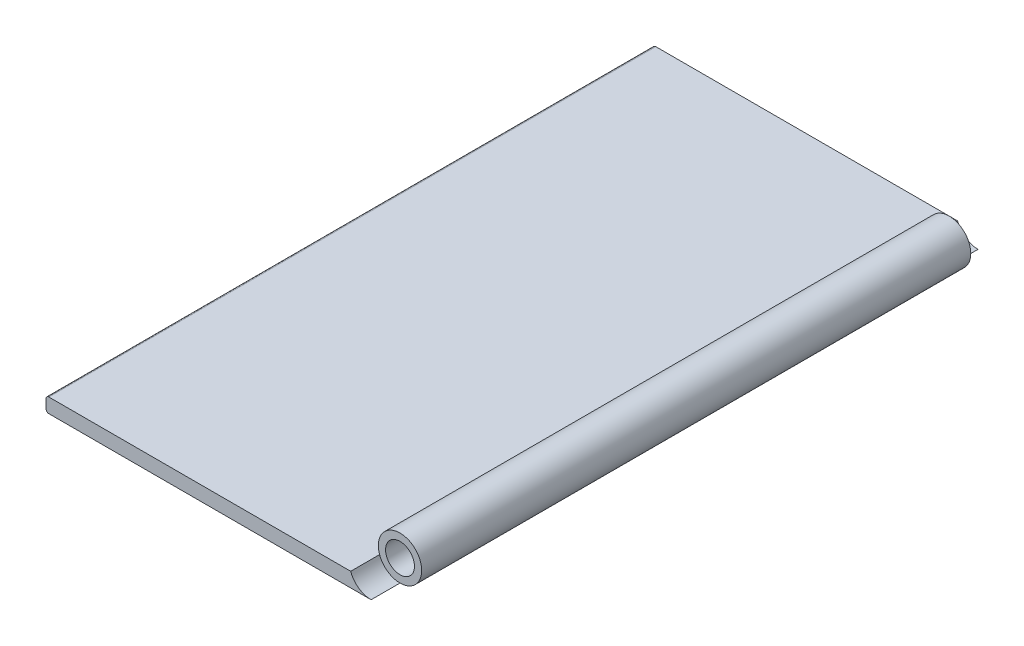
SolidWorks part; units mm, degrees
ref_plane "Front" through (0, 0, 0) normal (0, 0, 1) x (1, 0, 0)
ref_plane "Top" through (0, 0, 0) normal (0, 1, 0) x (1, 0, 0)
ref_plane "Right" through (0, 0, 0) normal (1, 0, 0) x (0, 0, -1)
sketch "草图1" plane through (0, 0, 0) normal (0, 0, 1) x (1, 0, 0)
  line L0 (112.7381, 241.1408) -> (1063.4047, 241.1408) construction
  line L1 (-1000, 0) -> (49000, 0) construction
  line L2 (-992.7821, 15) -> (49007.2179, 15) construction
  line L3 (0, -1000) -> (0, 5) construction
  line L4 (120, -895.6152) -> (120, 49104.3848) construction
  line L5 (210.9503, 181.969) -> (1161.617, 181.969) construction
  line L6 (1, 8) -> (85, 8)
  line L7 (1, 0) -> (120, 0)
  line L8 (0, 1) -> (0, 4)
  line L9 (1, 15) -> (120, 15)
  line L10 (120, 0) -> (120, 15)
  line L11 (85, 8) -> (85, 15)
  line L12 (1, 5) -> (100.0741, 5)
  line L13 (85, 8) -> (90.5674, 8) construction
  line L14 (90.5674, 8) -> (102.8766, 6.6995) construction
  line L15 (102.8766, 6.6995) -> (105.9196, 0) construction
  line L16 (105.9196, 0) -> (112.5, 0) construction
  line L17 (0, 8) -> (0, 49000) construction
  line L18 (0, 9) -> (0, 14)
  line L21 (100.0741, 5) -> (105.4289, 5)
  circle A0 centre (112.5, 7.5) radius 7.5
  arc A1 (1, 0) -> (0, 1) centre (1, 1) cw
  arc A2 (1, 5) -> (0, 4) centre (1, 4) ccw
  arc A3 (0, 14) -> (1, 15) centre (1, 14) cw
  arc A4 (1, 8) -> (0, 9) centre (1, 9) cw
  circle A5 centre (112.5, 7.5) radius 5
  spline S0 degree 4 poles (85, 8) (90.5674, 8) (102.8766, 6.6995) (105.9196, 0) (112.5, 0) knots 0 0 0 0 0 1 1 1 1 1
  point P30 (0, 0)
  point P36 (0, 15)
  dimension "D1" = 120
  dimension "D3" = 120
  dimension "D7" = 15
  dimension "D11" = 1
  dimension "D10" = 10
  dimension "D2" = 15
  dimension "D4" = 15
  dimension "D5" = 7
  dimension "D6" = 85
  dimension "D8" = 7.5
  dimension "D9" = 7.5
extrude "凸台-拉伸1" add sketch "草图1" along normal blind 210
sketch "草图2" plane through (0, 0, 210) normal (0, 0, 1) x (1, 0, 0)
  circle A0 centre (112.5, 7.5) radius 7.5
extrude "切除-拉伸1" cut sketch "草图2" against normal blind 10
sketch "草图3" plane through (0, 0, 0) normal (0, 0, -1) x (-1, 0, 0)
  circle A0 centre (-112.5, 7.5) radius 7.5
extrude "切除-拉伸2" cut sketch "草图3" against normal blind 10
